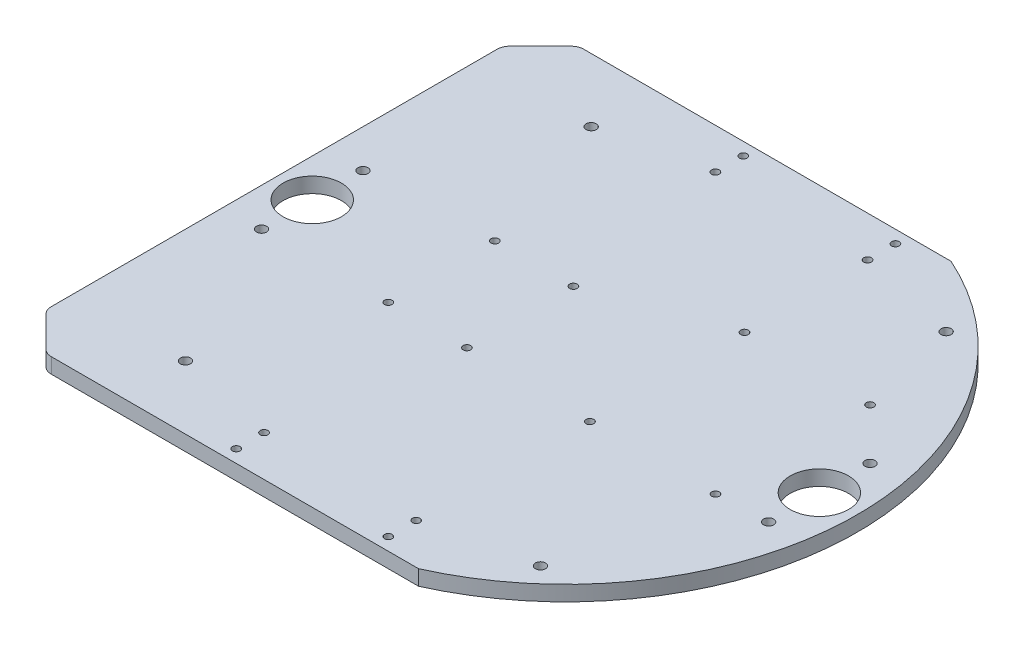
SolidWorks part; units mm, degrees
ref_plane "Front Plane" through (0, 0, 0) normal (0, 0, 1) x (1, 0, 0)
ref_plane "Top Plane" through (0, 0, 0) normal (0, 1, 0) x (1, 0, 0)
ref_plane "Right Plane" through (0, 0, 0) normal (1, 0, 0) x (0, 0, -1)
sketch "Sketch1" plane through (0, 0, 0) normal (0, 1, 0) x (1, 0, 0)
  line L0 (-150, 0) -> (150, 0) construction
  line L1 (-46.9042, -105) -> (46.9042, -105)
  line L2 (-46.9042, 105) -> (46.9042, 105)
  line L3 (-115, 0) -> (-115, 155.3364) construction
  line L4 (115, 0) -> (115, 153.7294) construction
  line L5 (-127.4755, 127.4755) -> (127.4755, -127.4755) construction
  line L6 (-127.4755, -127.4755) -> (127.4755, 127.4755) construction
  circle A0 centre (-30, 100) radius 1.5
  circle A1 centre (30, 100) radius 1.5
  circle A2 centre (30, 89) radius 1.5
  circle A3 centre (-30, 89) radius 1.5
  circle A4 centre (-30, -89) radius 1.5
  circle A5 centre (30, -89) radius 1.5
  circle A6 centre (30, -100) radius 1.5
  circle A7 centre (-30, -100) radius 1.5
  arc A8 (-46.9042, 105) -> (-46.9042, -105) centre (0, 0) ccw
  arc A9 (46.9042, -105) -> (46.9042, 105) centre (0, 0) ccw
  point P0 (0, 0)
  dimension "D3" = 3
  dimension "D10" = 230
  dimension "D1" = 100
  dimension "D2" = 105
  dimension "D4" = 105
  dimension "D7" = 30
  dimension "D8" = 11
  dimension "D9" = 60
  dimension "D11" = 5
  dimension "D12" = 85
  dimension "D13" = 85
  dimension "D14" = 115
  dimension "D15" = 45
  dimension "D16" = 45
  dimension "D5" = 2
  dimension "D6" = 2
extrude "Boss-Extrude2" add sketch "Sketch1" along normal blind 6
sketch "Sketch2" plane through (0, 6, 0) normal (0, 1, 0) x (1, 0, 0)
  line L0 (-115, 0) -> (115, 0) construction
  line L1 (-70, 80) -> (70, 80) construction
  line L2 (-70, 80) -> (-70, -80) construction
  line L3 (-70, -80) -> (70, -80) construction
  line L4 (70, 80) -> (70, -80) construction
  line L5 (-70, 80) -> (70, -80) construction
  line L6 (-70, -80) -> (70, 80) construction
  line L7 (0, 105) -> (0, -105) construction
  line L8 (46.9042, 105) -> (-46.9042, 105) construction
  line L9 (-46.9042, -105) -> (46.9042, -105) construction
  circle A0 centre (-50, 22) radius 1.5
  circle A1 centre (-19, 22) radius 1.5
  circle A2 centre (-19, -20) radius 1.5
  circle A3 centre (-50, -20) radius 1.5
  circle A4 centre (80, 40) radius 1.5
  circle A5 centre (30.47, 40) radius 1.5
  circle A6 centre (30.47, -20.96) radius 1.5
  circle A7 centre (80, -20.96) radius 1.5
  circle A8 centre (70, 80) radius 2
  circle A9 centre (-70, 80) radius 2
  circle A10 centre (-70, -80) radius 2
  circle A11 centre (70, -80) radius 2
  arc A12 (-46.9042, 105) -> (-46.9042, -105) centre (0, 0) ccw construction
  arc A13 (46.9042, -105) -> (46.9042, 105) centre (0, 0) ccw construction
  circle A14 centre (-100, 20) radius 2
  circle A15 centre (-100, -20) radius 2
  circle A16 centre (100, 20) radius 2
  circle A17 centre (100, -20) radius 2
  circle A18 centre (-100, 0) radius 11.5
  circle A19 centre (100, 0) radius 11.5
  point P5 (0, 0)
  dimension "D1" = 3
  dimension "D3" = 22
  dimension "D7" = 42
  dimension "D8" = 3
  dimension "D17" = 4
  dimension "D18" = 4
  dimension "D19" = 15
  dimension "D22" = 23
  dimension "D2" = 50
  dimension "D6" = 31
  dimension "D9" = 80
  dimension "D10" = 40
  dimension "D13" = 60.96
  dimension "D14" = 49.53
  dimension "D15" = 140
  dimension "D16" = 160
  dimension "D20" = 20
  dimension "D21" = 20
  dimension "D4" = 2
  dimension "D5" = 2
  dimension "D11" = 2
  dimension "D12" = 2
extrude "Cut-Extrude1" cut sketch "Sketch2" against normal blind 6
ref_plane "Plane1" through (0, 6, 0) normal (0, 1, 0) x (1, 0, 0)
sketch "Sketch4" plane through (0, 6, 0) normal (0, 1, 0) x (1, 0, 0)
  line L0 (-46.9042, 105) -> (-115, 105)
  line L1 (-46.9042, -105) -> (-115, -105)
  line L2 (-115, -105) -> (-115, 105)
  arc A1 (-46.9042, 105) -> (-46.9042, -105) centre (0, 0) ccw construction
  arc A2 (-46.9042, 105) -> (-46.9042, -105) centre (0, 0) ccw
  dimension "D1" = 68.0958
extrude "Boss-Extrude3" add sketch "Sketch4" against normal blind 6 contours A2 L0 L2 | A2 L2 L1
chamfer "Chamfer1" distance 15 angle 45 2 edges at (-115, 3, 105) (-115, 3, -105)
fillet "Fillet1" radius 5 4 edges at (-100, 3, -105) (-115, 3, -90) (-100, 3, 105) (-115, 3, 90)
